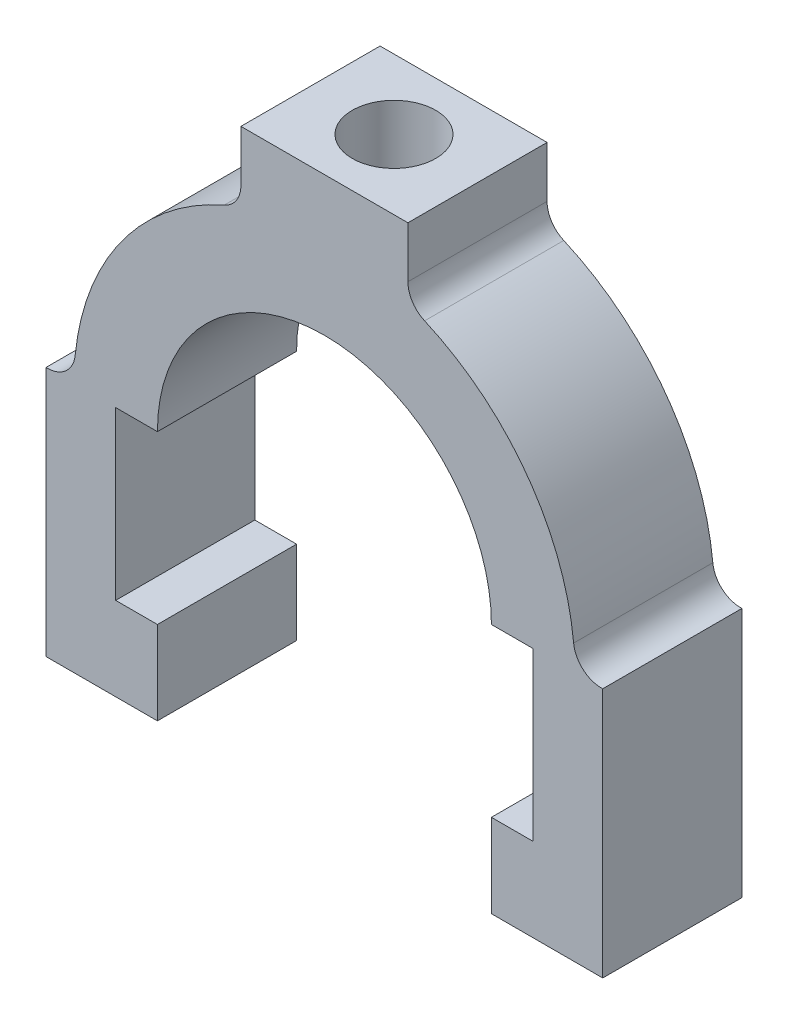
SolidWorks part; units mm, degrees
ref_plane "Front Plane" through (0, 0, 0) normal (0, 0, 1) x (1, 0, 0)
ref_plane "Top Plane" through (0, 0, 0) normal (0, 1, 0) x (1, 0, 0)
ref_plane "Right Plane" through (0, 0, 0) normal (1, 0, 0) x (0, 0, -1)
sketch "Sketch1" plane through (0, 0, 0) normal (0, 0, 1) x (1, 0, 0)
  line L0 (0, 0) -> (0, 2032) construction
  line L1 (-304.8, 2032) -> (304.8, 2032)
  line L2 (304.8, 2032) -> (304.8, 1845.5794)
  line L3 (-304.8, 2032) -> (-304.8, 1845.5794)
  line L4 (1016, 914.4) -> (1016, 0)
  line L5 (-1016, 914.4) -> (-1016, 0)
  line L6 (1016, 0) -> (609.6, 0)
  line L7 (-1016, 0) -> (-609.6, 0)
  line L8 (609.6, 0) -> (609.6, 304.8)
  line L9 (-609.6, 0) -> (-609.6, 304.8)
  line L10 (609.6, 304.8) -> (762, 304.8)
  line L11 (-609.6, 304.8) -> (-762, 304.8)
  line L12 (762, 304.8) -> (762, 914.4)
  line L13 (-762, 304.8) -> (-762, 914.4)
  line L14 (762, 914.4) -> (609.6, 914.4)
  line L15 (-762, 914.4) -> (-609.6, 914.4)
  arc A0 (304.8, 1845.5794) -> (365.76, 1752.4614) centre (406.4, 1845.5794) ccw
  arc A1 (-304.8, 1845.5794) -> (-365.76, 1752.4614) centre (-406.4, 1845.5794) cw
  arc A2 (365.76, 1752.4614) -> (909.828, 1005.7256) centre (0, 914.4) cw
  arc A3 (-365.76, 1752.4614) -> (-909.828, 1005.7256) centre (0, 914.4) ccw
  arc A4 (909.828, 1005.7256) -> (1016, 914.4) centre (1010.92, 1015.8729) ccw
  arc A5 (-909.828, 1005.7256) -> (-1016, 914.4) centre (-1010.92, 1015.8729) cw
  arc A6 (609.6, 914.4) -> (-609.6, 914.4) centre (0, 914.4) ccw
  point P32 (0, 0)
  point P33 (0, 0)
  dimension "D1" = 609.6
  dimension "D2" = 914.4
  dimension "D6" = 101.6
  dimension "D3" = 609.6
  dimension "D4" = 2032
  dimension "D5" = 914.4
  dimension "D7" = 101.6
  dimension "D8" = 254
  dimension "D9" = 406.4
  dimension "D10" = 304.8
extrude "Boss-Extrude1" add sketch "Sketch1" along normal mid plane 508
sketch "Sketch2" plane through (0, 2032, 0) normal (0, 1, 0) x (1, 0, 0)
  circle A0 centre (0, 0) radius 152.4
  dimension "D1" = 304.8
extrude "Cut-Extrude1" cut sketch "Sketch2" against normal through all
